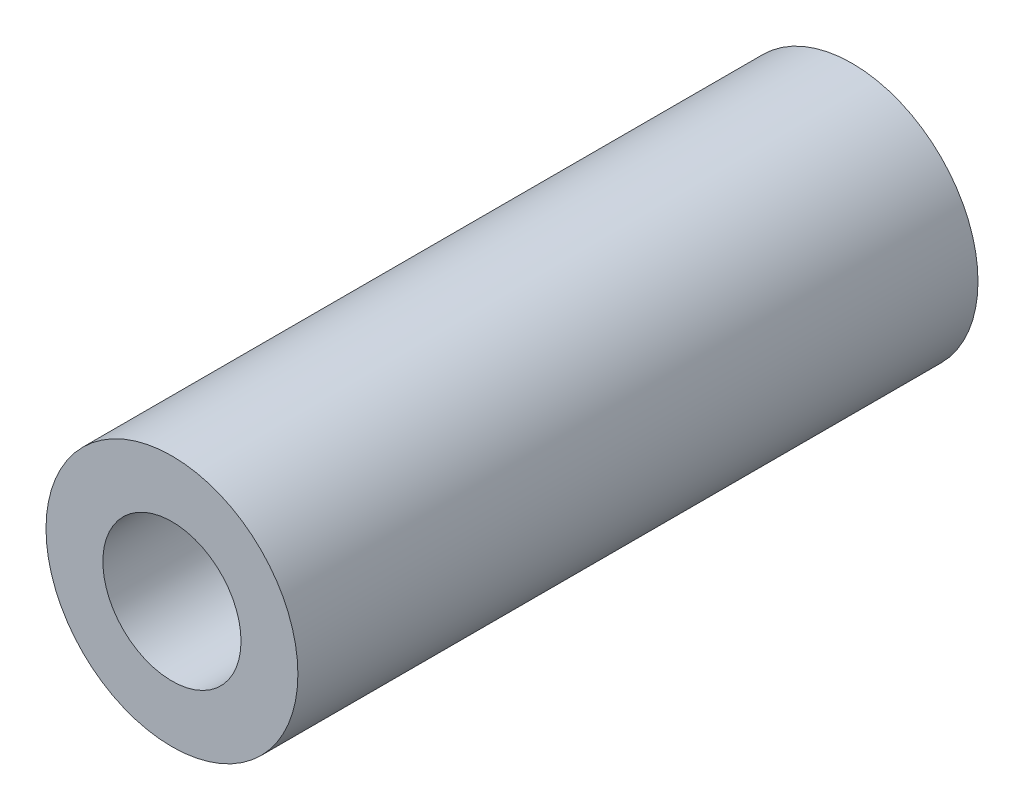
SolidWorks part; units mm, degrees
material "ABS"
ref_plane "Plano frontal" through (0, 0, 0) normal (0, 0, 1) x (1, 0, 0)
ref_plane "Plano superior" through (0, 0, 0) normal (0, 1, 0) x (1, 0, 0)
ref_plane "Plano direito" through (0, 0, 0) normal (1, 0, 0) x (0, 0, -1)
sketch "Esboço1" plane through (0, 0, 0) normal (0, 0, 1) x (1, 0, 0)
  circle A0 centre (16.0167, 16.0167) radius 3.1
  circle A1 centre (16.0167, 16.0167) radius 1.55
  dimension "D1" = 3.1
extrude "Ressalto-extrusão1" add sketch "Esboço1" along normal up to vertex (16.74 mm away)
hole_wizard "M3 Clearance Hole1" positions "3DSketch1" profile "Sketch1" hole size "M3" standard "ISO" end condition through all
sketch3d "3DSketch1"
  line L0 (16.0167, 16.0167, 16.74) -> (16.0167, 16.0167, 0) construction
  line L1 (16.0167, 16.0167, 16.74) -> (16.0167, 16.0167, 0) construction
  point P0 (16.0167, 16.0167, 16.74)
sketch "Sketch1" plane through (16.0167, 16.0167, 16.74) normal (1, 0, 0) x (0, -1, 0)
  line L0 (0, 0) -> (0, 16.74)
  line L1 (0, 16.74) -> (1.7, 16.74)
  line L2 (1.7, 16.74) -> (1.7, 0)
  line L5 (1.7, 0) -> (0, 0)
  line L11 (0, -6.35) -> (0, 107.95) construction
  dimension "Thru Hole Dia." = 3.4
  dimension "Thru Hole Depth" = 16.74
